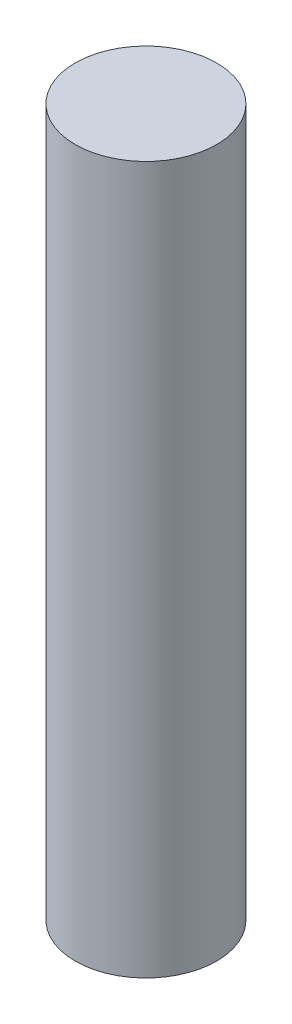
SolidWorks part; units mm, degrees
ref_plane "Alzado" through (0, 0, 0) normal (0, 0, 1) x (1, 0, 0)
ref_plane "Planta" through (0, 0, 0) normal (0, 1, 0) x (1, 0, 0)
ref_plane "Vista lateral" through (0, 0, 0) normal (1, 0, 0) x (0, 0, -1)
sketch "Croquis1" plane through (0, 0, 0) normal (0, 1, 0) x (1, 0, 0)
  circle A0 centre (0, 0) radius 5
  dimension "D1" = 10
extrude "Saliente-Extruir1" add sketch "Croquis1" along normal blind 50
